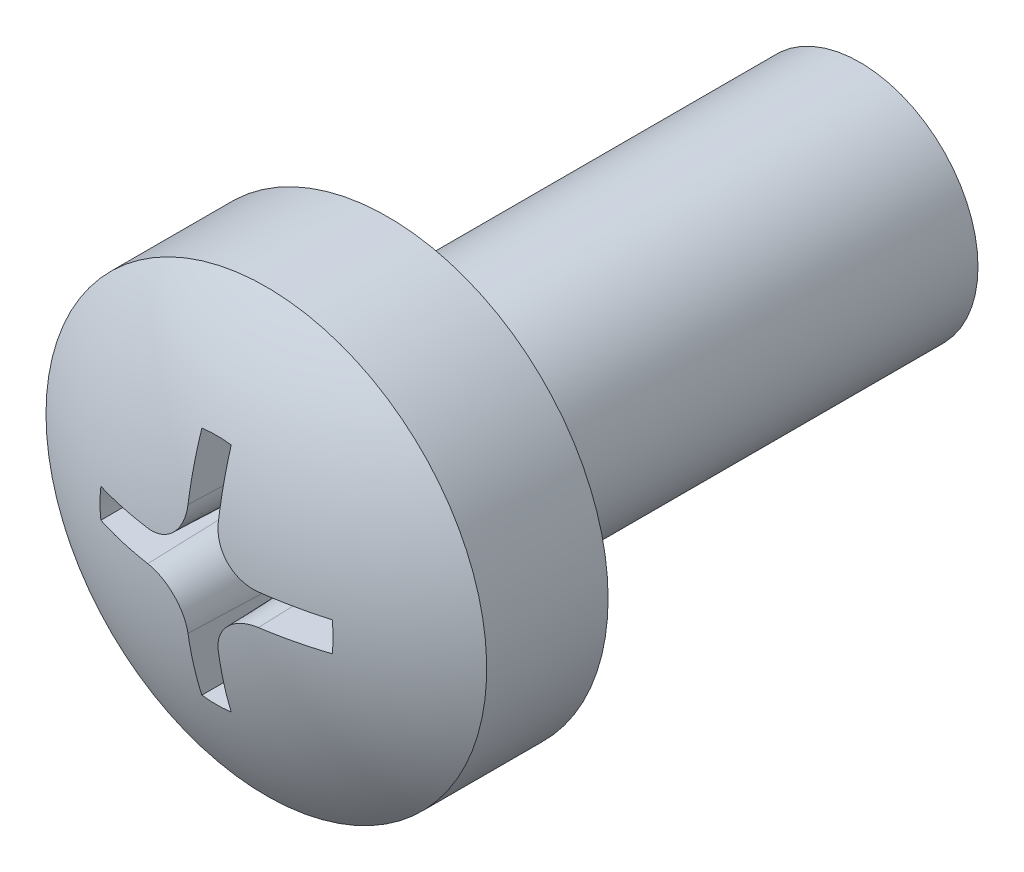
SolidWorks part; units mm, degrees
material "普通碳钢"
ref_plane "Plane1" through (0, 0, 0) normal (0, 0, 1) x (1, 0, 0)
ref_plane "Plane2" through (0, 0, 0) normal (0, 1, 0) x (1, 0, 0)
ref_plane "Plane3" through (0, 0, 0) normal (1, 0, 0) x (0, 0, -1)
sketch "Sketch1" plane through (0, 0, 0) normal (0, 0, 1) x (1, 0, 0)
  circle A0 centre (0, 0) radius 1.5
  dimension "D1" = 3
extrude "Base-Extrude" add sketch "Sketch1" along normal blind 6
sketch "Sketch6" plane through (0, 0, 0) normal (0, 1, 0) x (1, 0, 0)
  line L0 (0, 0.3936) -> (0, -34.4908) construction
  line L1 (0, -6) -> (0, 0) construction
  line L2 (0, -6) -> (2.8, -6)
  line L3 (2.8, -6) -> (2.8, -7.5425)
  line L4 (0, -8.4) -> (0, -6)
  line L5 (-1.5, -6) -> (1.5, -6) construction
  arc A0 (2.8, -7.5425) -> (0, -8.4) centre (0, -3.4) cw
  dimension "D1" = 2.4
  dimension "D9" = 5
  dimension "D8" = 2.8
revolve "Boss-Revolve2" add sketch "Sketch6" angle 360 about L0
ref_plane "Plane6" through (0, 0, 8.7) normal (0, 0, -1) x (-1, 0, 0)
sketch "Sketch7" plane through (0, 0, 8.7) normal (0, 0, -1) x (-1, 0, 0)
  line L0 (-7.1, 0) -> (5.9, 0) construction
  line L1 (0, 7.5) -> (0, -7) construction
  line L2 (0.205, 1.4859) -> (0.205, 0.7082)
  line L3 (0, 0) -> (4.9858, 4.9858) construction
  line L4 (1.4859, 0.205) -> (0.703, 0.2082)
  line L5 (1.4859, -0.205) -> (0.703, -0.2082)
  line L6 (0.205, -1.4859) -> (0.205, -0.7082)
  line L7 (-0.205, -1.4859) -> (-0.205, -0.7082)
  line L8 (-1.4859, -0.205) -> (-0.703, -0.2082)
  line L9 (-1.4859, 0.205) -> (-0.703, 0.2082)
  line L10 (-0.205, 1.4859) -> (-0.205, 0.7082)
  arc A0 (-0.205, 1.4859) -> (0.205, 1.4859) centre (0, 0) cw
  arc A1 (1.4859, -0.205) -> (1.4859, 0.205) centre (0, 0) ccw
  arc A2 (0.205, 0.7082) -> (0.703, 0.2082) centre (0.705, 0.7082) ccw
  arc A3 (-0.205, 0.7082) -> (-0.703, 0.2082) centre (-0.705, 0.7082) cw
  arc A4 (-0.205, -1.4859) -> (0.205, -1.4859) centre (0, 0) ccw
  arc A5 (-0.205, -0.7082) -> (-0.703, -0.2082) centre (-0.705, -0.7082) ccw
  arc A6 (-1.4859, -0.205) -> (-1.4859, 0.205) centre (0, 0) cw
  arc A7 (0.703, -0.2082) -> (0.205, -0.7082) centre (0.705, -0.7082) ccw
  dimension "D1" = 0.5
  dimension "D10" = 1.5
  dimension "D11" = 0.41
extrude "Cut-Extrude1" cut sketch "Sketch7" along normal blind 1.8 draft 2
